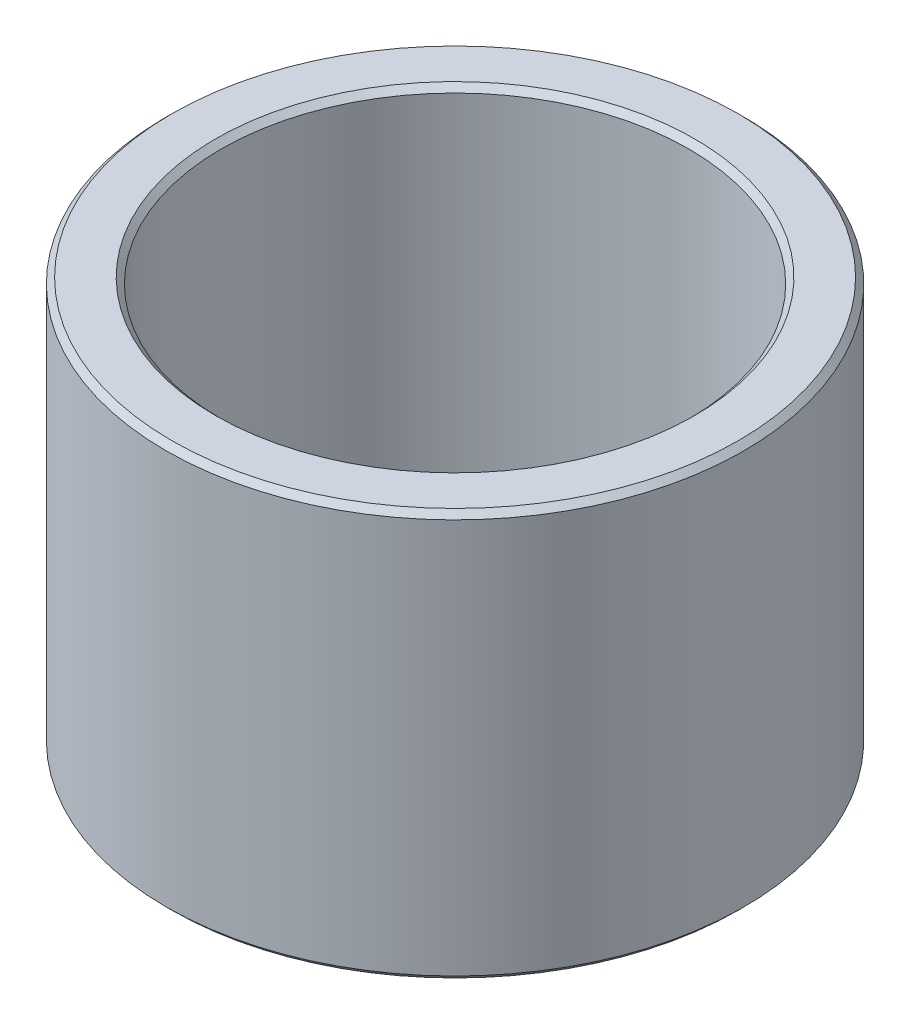
SolidWorks part; units mm, degrees
material "Plain Carbon Steel"
ref_plane "Front Plane" through (0, 0, 0) normal (0, 0, 1) x (1, 0, 0)
ref_plane "Top Plane" through (0, 0, 0) normal (0, 1, 0) x (1, 0, 0)
ref_plane "Right Plane" through (0, 0, 0) normal (1, 0, 0) x (0, 0, -1)
sketch "Sketch1" plane through (0, 0, 0) normal (0, 1, 0) x (1, 0, 0)
  circle A0 centre (0, 0) radius 4.975
  circle A1 centre (0, 0) radius 4.025
  dimension "D1" = 9.95
  dimension "D2" = 8.05
extrude "Boss-Extrude1" add sketch "Sketch1" along normal mid plane 7
chamfer "Chamfer1" distance 0.1 angle 45 4 edges at (0, -3.5, 4.975) (0, 3.5, 4.975) (0, -3.5, 4.025) (0, 3.5, 4.025)
